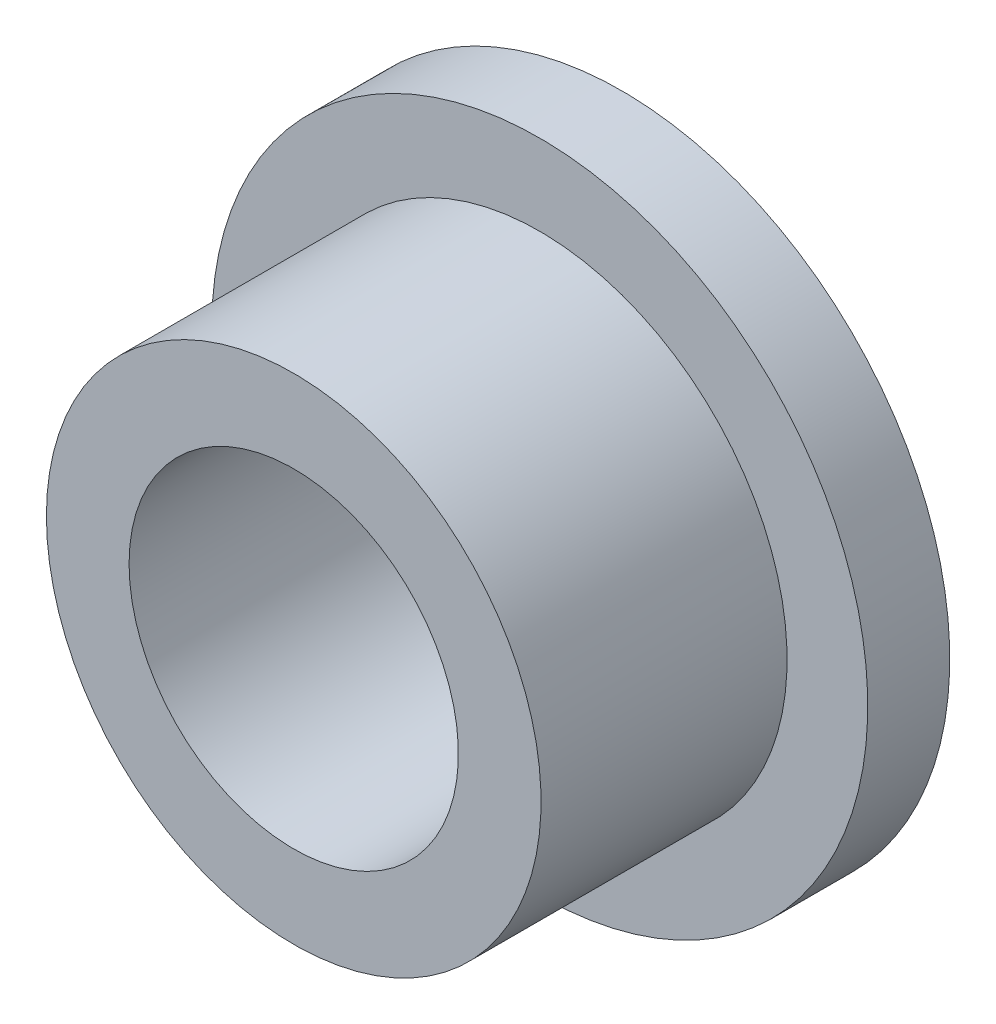
SolidWorks part; units mm, degrees
ref_plane "前视基准面" through (0, 0, 0) normal (0, 0, 1) x (1, 0, 0)
ref_plane "上视基准面" through (0, 0, 0) normal (0, 1, 0) x (1, 0, 0)
ref_plane "右视基准面" through (0, 0, 0) normal (1, 0, 0) x (0, 0, -1)
ref_plane "基准面4" through (0, 0, 0) normal (0, -1, 0) x (1, 0, 0)
sketch "草图1" plane through (0, 0, 0) normal (0, -1, 0) x (1, 0, 0)
  line L0 (3.1877, 6.35) -> (3.1877, 0)
  line L1 (3.1877, 0) -> (6.35, 0)
  line L2 (6.35, 0) -> (6.35, 1.5875)
  line L3 (6.35, 1.5875) -> (4.7879, 1.5875)
  line L4 (4.7879, 1.5875) -> (4.7879, 6.35)
  line L5 (4.7879, 6.35) -> (3.1877, 6.35)
  line L6 (0, 6.35) -> (0, 0) construction
revolve "旋转1" add sketch "草图1" angle 360 about L6
